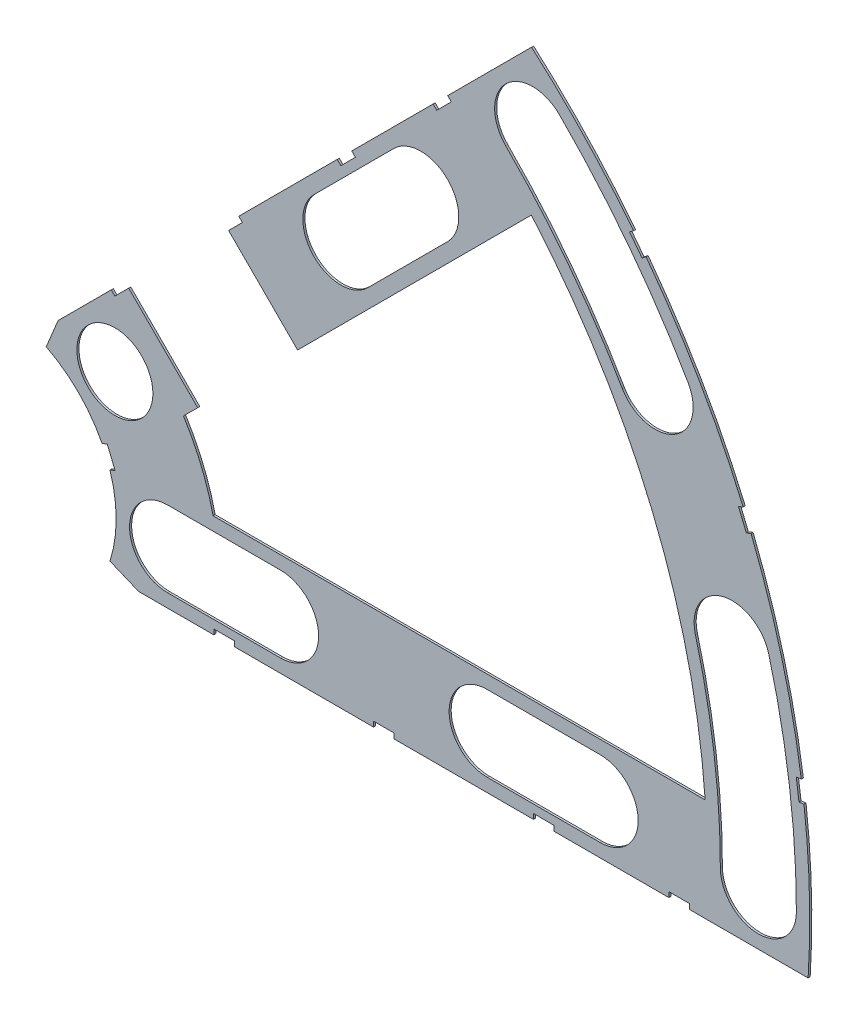
SolidWorks part; units mm, degrees
material "PTFE (general)"
ref_plane "Front Plane" through (0, 0, 0) normal (0, 0, 1) x (1, 0, 0)
ref_plane "Top Plane" through (0, 0, 0) normal (0, 1, 0) x (1, 0, 0)
ref_plane "Right Plane" through (0, 0, 0) normal (1, 0, 0) x (0, 0, -1)
sketch "Sketch1" plane through (0, 0, 0) normal (0, 0, 1) x (1, 0, 0)
  line L0 (0, 0) -> (320.3893, 0) construction
  line L1 (0, 0) -> (155.5285, 155.5285) construction
  line L2 (67.2115, 76.1917) -> (8.6967, 17.6769)
  line L3 (8.6967, 17.6769) -> (7.229, 14.1336)
  line L4 (101.4014, -6.35) -> (18.6489, -6.35)
  line L5 (15.1056, -4.8823) -> (18.6489, -6.35)
  line L6 (88.6729, 6.35) -> (27.8605, 6.35)
  line L9 (67.1914, 58.2111) -> (24.1905, 15.2102)
  line L10 (0, 0) -> (40.4486, 97.6516) construction
  line L11 (0, 0) -> (123.4567, -51.1374) construction
  line L18 (8.6967, 17.6769) -> (13.294, 8.6183) construction
  line L19 (18.6489, -6.35) -> (15.4943, 3.3063) construction
  line L20 (27.8605, 6.35) -> (27.7442, 6.7059) construction
  line L21 (24.1905, 15.2102) -> (24.3599, 14.8764) construction
  arc A0 (7.229, 14.1336) -> (15.1056, -4.8823) centre (0, 0) cw
  arc A1 (67.2115, 76.1917) -> (101.4014, -6.35) centre (0, 0) cw
  arc A2 (24.1905, 15.2102) -> (27.8605, 6.35) centre (0, 0) cw
  arc A3 (67.1914, 58.2111) -> (88.6729, 6.35) centre (0, 0) cw
  arc A8 (13.294, 8.6183) -> (15.4943, 3.3063) centre (0, 0) cw construction
  arc A9 (24.3599, 14.8764) -> (27.7442, 6.7059) centre (0, 0) cw construction
  dimension "D1" = 45
  dimension "D3" = 6.35
  dimension "D4" = 15.875
  dimension "D7" = 22.5
  dimension "D8" = 101.6
  dimension "D11" = 12.7
  dimension "D12" = 12.7
  dimension "D2" = 6.35
  dimension "D5" = 67.5
  dimension "D9" = 1.27
  dimension "D10" = 1.27
  dimension "D6" = 12.7
extrude "Boss-Extrude1" add sketch "Sketch1" along normal blind 0.254
sketch "Sketch2" plane through (0, 0, 0.254) normal (0, 0, 1) x (1, 0, 0)
  line L0 (0, 0) -> (101.6, 0) construction
  line L1 (0, 0) -> (71.842, 71.842) construction
  line L3 (0, 0) -> (22.225, 0) construction
  line L4 (0, 0) -> (15.7154, 15.7154) construction
  line L5 (0, 0) -> (95.25, 0) construction
  line L6 (0, 0) -> (92.0044, 24.6525) construction
  arc A0 (101.4014, -6.35) -> (67.2115, 76.1917) centre (0, 0) ccw construction
  circle A1 centre (22.225, 0) radius 4.699
  arc A2 (15.1056, -4.8823) -> (7.229, 14.1336) centre (0, 0) ccw construction
  circle A3 centre (36.195, 0) radius 4.699
  circle A4 centre (61.722, 0) radius 4.699
  circle A5 centre (75.692, 0) radius 4.699
  circle A6 centre (95.25, 0) radius 4.699
  circle A7 centre (15.7154, 15.7154) radius 4.699
  circle A8 centre (25.5937, 25.5937) radius 4.699
  circle A9 centre (43.644, 43.644) radius 4.699
  circle A10 centre (53.5223, 53.5223) radius 4.699
  circle A11 centre (92.0044, 24.6525) radius 4.699
  circle A12 centre (82.4889, 47.625) radius 4.699
  circle A13 centre (67.3519, 67.3519) radius 4.699
  dimension "D3" = 9.398
  dimension "D1" = 45
  dimension "D2" = 6.35
  dimension "D4" = 6.35
  dimension "D5" = 13.97
  dimension "D7" = 13.97
  dimension "D8" = 19.558
  dimension "D9" = 45
  dimension "D10" = 15
  dimension "D11" = 25.527
  dimension "D6" = 2
extrude "Cut-Extrude1" cut sketch "Sketch2" against normal through all
sketch "Sketch3" plane through (0, 0, 0.254) normal (0, 0, 1) x (1, 0, 0)
  line L0 (15.2664, 24.2467) -> (17.0625, 26.0427)
  line L1 (15.2664, 24.2467) -> (15.7154, 23.7977)
  line L2 (17.0625, 26.0427) -> (17.5115, 25.5937)
  line L3 (15.7154, 23.7977) -> (17.5115, 25.5937)
  line L4 (67.2115, 76.1917) -> (8.6967, 17.6769) construction
  line L5 (44.9911, 53.9713) -> (43.195, 52.1753)
  line L6 (44.9911, 53.9713) -> (45.4401, 53.5223)
  line L7 (43.195, 52.1753) -> (43.644, 51.7263)
  line L8 (45.4401, 53.5223) -> (43.644, 51.7263)
  line L9 (27.94, -6.35) -> (30.48, -6.35)
  line L10 (27.94, -6.35) -> (27.94, -5.715)
  line L11 (30.48, -6.35) -> (30.48, -5.715)
  line L12 (27.94, -5.715) -> (30.48, -5.715)
  line L13 (18.6489, -6.35) -> (101.4014, -6.35) construction
  line L14 (67.437, -6.35) -> (69.977, -6.35)
  line L15 (67.437, -6.35) -> (67.437, -5.715)
  line L16 (69.977, -6.35) -> (69.977, -5.715)
  line L17 (67.437, -5.715) -> (69.977, -5.715)
  line L18 (29.2307, 38.211) -> (31.0268, 40.007)
  line L19 (29.2307, 38.211) -> (29.6797, 37.762)
  line L20 (31.0268, 40.007) -> (31.4758, 39.558)
  line L21 (29.6797, 37.762) -> (31.4758, 39.558)
  line L22 (56.845, 65.8253) -> (55.049, 64.0292)
  line L23 (56.845, 65.8253) -> (57.294, 65.3763)
  line L24 (55.049, 64.0292) -> (55.498, 63.5802)
  line L25 (57.294, 65.3763) -> (55.498, 63.5802)
  line L26 (47.6885, -6.35) -> (50.2285, -6.35)
  line L27 (47.6885, -6.35) -> (47.6885, -5.715)
  line L28 (50.2285, -6.35) -> (50.2285, -5.715)
  line L29 (47.6885, -5.715) -> (50.2285, -5.715)
  line L30 (84.201, -6.35) -> (86.741, -6.35)
  line L31 (84.201, -6.35) -> (84.201, -5.715)
  line L32 (86.741, -6.35) -> (86.741, -5.715)
  line L33 (84.201, -5.715) -> (86.741, -5.715)
  line L34 (0, 0) -> (100.7308, 13.2615) construction
  line L35 (0, 0) -> (93.8662, 38.8806) construction
  line L36 (0, 0) -> (80.6047, 61.8502) construction
  line L37 (0, 0) -> (101.6, 0) construction
  line L38 (99.9355, 14.4377) -> (100.267, 11.9194)
  line L39 (99.9355, 14.4377) -> (101.1946, 14.6035)
  line L40 (100.267, 11.9194) -> (101.5261, 12.0852)
  line L41 (101.1946, 14.6035) -> (101.5261, 12.0852)
  line L42 (99.9355, 14.4377) -> (101.5261, 12.0852) construction
  line L43 (100.267, 11.9194) -> (101.1946, 14.6035) construction
  line L44 (93.7655, 37.4643) -> (94.9388, 37.9503)
  line L45 (93.7655, 37.4643) -> (92.7935, 39.811)
  line L46 (94.9388, 37.9503) -> (93.9668, 40.297)
  line L47 (92.7935, 39.811) -> (93.9668, 40.297)
  line L48 (93.7655, 37.4643) -> (93.9668, 40.297) construction
  line L49 (94.9388, 37.9503) -> (92.7935, 39.811) construction
  line L50 (79.3278, 62.4712) -> (80.874, 60.456)
  line L51 (79.3278, 62.4712) -> (80.3354, 63.2443)
  line L52 (80.874, 60.456) -> (81.8816, 61.2292)
  line L53 (80.3354, 63.2443) -> (81.8816, 61.2292)
  line L54 (79.3278, 62.4712) -> (81.8816, 61.2292) construction
  line L55 (80.874, 60.456) -> (80.3354, 63.2443) construction
  line L56 (13.5939, 7.0054) -> (14.5659, 4.6588)
  line L57 (13.5939, 7.0054) -> (14.7672, 7.4914)
  line L58 (14.5659, 4.6588) -> (15.7393, 5.1448)
  line L59 (14.7672, 7.4914) -> (15.7393, 5.1448)
  line L60 (13.5939, 7.0054) -> (15.7393, 5.1448) construction
  line L61 (14.5659, 4.6588) -> (14.7672, 7.4914) construction
  circle A0 centre (15.7154, 15.7154) radius 4.699 construction
  circle A1 centre (43.644, 43.644) radius 4.699 construction
  circle A2 centre (22.225, 0) radius 4.699 construction
  circle A3 centre (61.722, 0) radius 4.699 construction
  arc A4 (101.4014, -6.35) -> (67.2115, 76.1917) centre (0, 0) ccw construction
  arc A9 (15.1056, -4.8823) -> (7.229, 14.1336) centre (0, 0) ccw construction
  circle A10 centre (36.195, 0) radius 4.699 construction
  circle A11 centre (75.692, 0) radius 4.699 construction
  circle A12 centre (25.5937, 25.5937) radius 4.699 construction
  circle A13 centre (53.5223, 53.5223) radius 4.699 construction
  point P75 (14.6666, 6.0751)
  dimension "D2" = 5.715
  dimension "D3" = 2.54
  dimension "D6" = 5.715
  dimension "D8" = 0.635
  dimension "D9" = 5.715
  dimension "D12" = 5.715
  dimension "D4" = 7.5
  dimension "D5" = 22.5
  dimension "D7" = 37.5
  dimension "D10" = 90
  dimension "D11" = 1.27
  dimension "D14" = 0.635
  dimension "D15" = 90
  dimension "D18" = 0.635
  dimension "D19" = 90
  dimension "D22" = 0.635
  dimension "D20" = 1.27
  dimension "D17" = 0.635
  dimension "D13" = 11.4935
  dimension "D16" = 8.509
  dimension "D21" = 11.4935
  dimension "D23" = 8.509
extrude "Cut-Extrude2" cut sketch "Sketch3" against normal through all
sketch "Sketch5" plane through (0, 0, 0.254) normal (0, 0, 1) x (1, 0, 0)
  line L0 (14.2786, 28.647) -> (26.6265, 40.9949)
  line L4 (14.2786, 28.647) -> (28.647, 14.2786)
  line L8 (26.6265, 40.9949) -> (40.9949, 26.6265)
  line L9 (28.647, 14.2786) -> (40.9949, 26.6265)
  line L12 (15.2664, 24.2467) -> (15.7154, 23.7977) construction
  line L13 (31.4758, 39.558) -> (31.0268, 40.007) construction
  circle A0 centre (25.5937, 25.5937) radius 4.699 construction
  dimension "D1" = 2.413
  dimension "D2" = 2.413
  dimension "D3" = 10.16
  dimension "D4" = 20.32
sketch "Sketch6" plane through (0, 0, 0.254) normal (0, 0, 1) x (1, 0, 0)
  line L0 (0, 0) -> (101.6, 0) construction
  line L1 (0, 0) -> (71.842, 71.842) construction
  line L2 (0, 0) -> (87.9882, 50.8) construction
  line L3 (0, 0) -> (98.1381, 26.296) construction
  line L7 (43.644, 43.644) -> (53.5223, 53.5223) construction
  line L8 (40.3213, 46.9667) -> (50.1996, 56.845)
  line L9 (46.9667, 40.3213) -> (56.845, 50.1996)
  line L10 (22.225, 0) -> (36.195, 0) construction
  line L11 (22.225, 4.699) -> (36.195, 4.699)
  line L12 (22.225, -4.699) -> (36.195, -4.699)
  line L13 (61.722, 0) -> (75.692, 0) construction
  line L14 (61.722, 4.699) -> (75.692, 4.699)
  line L15 (61.722, -4.699) -> (75.692, -4.699)
  arc A0 (79.8253, 62.8529) -> (67.2115, 76.1917) centre (0, 0) ccw construction
  circle A1 centre (53.5223, 53.5223) radius 4.699 construction
  arc A3 (40.3213, 46.9667) -> (46.9667, 40.3213) centre (43.644, 43.644) ccw
  arc A4 (56.845, 50.1996) -> (50.1996, 56.845) centre (53.5223, 53.5223) ccw
  arc A5 (101.4014, -6.35) -> (100.8887, 12.0013) centre (0, 0) ccw construction
  arc A6 (22.225, 4.699) -> (22.225, -4.699) centre (22.225, 0) ccw
  arc A7 (93.3728, 40.0509) -> (81.3715, 60.8378) centre (0, 0) ccw construction
  arc A8 (100.5572, 14.5196) -> (94.3448, 37.7043) centre (0, 0) ccw construction
  arc A9 (36.195, -4.699) -> (36.195, 4.699) centre (36.195, 0) ccw
  arc A10 (61.722, 4.699) -> (61.722, -4.699) centre (61.722, 0) ccw
  arc A11 (75.692, -4.699) -> (75.692, 4.699) centre (75.692, 0) ccw
  arc A12 (95.25, 0) -> (92.0044, 24.6525) centre (0, 0) ccw construction
  arc A13 (99.949, 0) -> (96.5433, 25.8687) centre (0, 0) ccw
  arc A14 (90.551, 0) -> (87.4655, 23.4363) centre (0, 0) ccw
  arc A15 (90.551, 0) -> (99.949, 0) centre (95.25, 0) ccw
  arc A16 (96.5433, 25.8687) -> (87.4655, 23.4363) centre (92.0044, 24.6525) ccw
  arc A17 (82.4889, 47.625) -> (67.3519, 67.3519) centre (0, 0) ccw construction
  arc A18 (86.5584, 49.9745) -> (70.6746, 70.6746) centre (0, 0) ccw
  arc A19 (78.4195, 45.2755) -> (64.0292, 64.0292) centre (0, 0) ccw
  arc A20 (78.4195, 45.2755) -> (86.5584, 49.9745) centre (82.4889, 47.625) ccw
  arc A21 (70.6746, 70.6746) -> (64.0292, 64.0292) centre (67.3519, 67.3519) ccw
  point P13 (48.5832, 48.5832)
  point P37 (29.21, 0)
  point P48 (68.707, 0)
  point P61 (94.4351, 12.4326)
  point P68 (75.5669, 57.9845)
  dimension "D3" = 9.398
  dimension "D4" = 9.398
  dimension "D1" = 45
  dimension "D2" = 9.398
  dimension "D5" = 9.398
extrude "Cut-Extrude4" cut sketch "Sketch6" against normal through all
extrude "Cut-Extrude5" cut sketch "Sketch5" against normal through all
equation "\"cSep\"= 1.005"
equation "\"D11@Sketch2\"=\"cSep\""
equation "\"cSep2\"= \"D8@Sketch2\""
equation "\"D13@Sketch3\"=\"cSep\"/2-.05"
equation "\"D16@Sketch3\"=\"cSep2\"/2-.05"
equation "\"D21@Sketch3\"=\"cSep\"/2-.05"
equation "\"D23@Sketch3\"=\"cSep2\"/2-.05"
